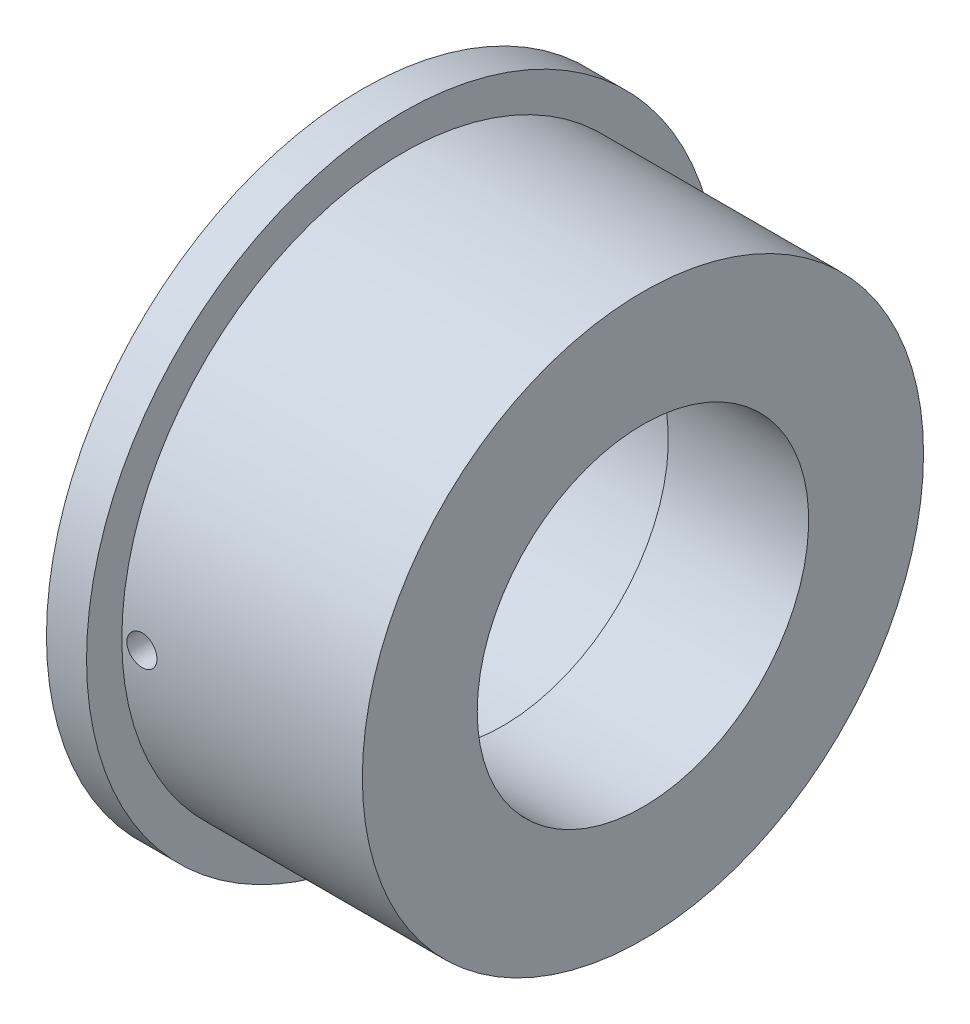
SolidWorks part; units mm, degrees
ref_plane "Front Plane" through (0, 0, 0) normal (0, 0, 1) x (1, 0, 0)
ref_plane "Top Plane" through (0, 0, 0) normal (0, 1, 0) x (1, 0, 0)
ref_plane "Right Plane" through (0, 0, 0) normal (1, 0, 0) x (0, 0, -1)
sketch "Sketch0" plane through (0, 0, 0) normal (0, 0, 1) x (1, 0, 0)
  line L0 (-44.45, 0) -> (0, 0) construction
  line L2 (-38.1, 44.45) -> (-38.1, -44.45) construction
  line L3 (-38.1, 50.038) -> (-38.1, -50.038) construction
  line L4 (-44.45, 34.3535) -> (-44.45, -34.3535) construction
  line L5 (-22.225, 30.099) -> (-44.45, 30.2895) construction
  line L6 (-22.225, 30.099) -> (-22.225, -30.099) construction
  line L7 (-22.225, -30.099) -> (-44.45, -30.2895) construction
  line L8 (-44.45, 30.2895) -> (-44.45, -30.2895) construction
  line L14 (-22.225, 26.2509) -> (-22.225, -26.2509) construction
  line L15 (-22.225, -26.2509) -> (-22.225, -30.3149) construction
  line L16 (-44.45, -30.2895) -> (-44.45, -34.3535) construction
  line L21 (-44.45, 0) -> (-22.225, 0) construction
  point P12 (-38.1, 0)
  dimension "A" = 44.45
  dimension "OD A 2" = 60.579
  dimension "OD B 2" = 60.198
  dimension "ID 2" = 52.5018
  dimension "H 2" = 4.064
  dimension "B" = 22.225
  dimension "Pipe OD 1" = 88.9
  dimension "C 1" = 38.1
  dimension "H 1" = 5.588
sketch "Sketch1" plane through (0, 0, 0) normal (0, 0, 1) x (1, 0, 0)
  line L0 (-44.45, 0) -> (0, 0) construction
  line L1 (-44.45, 0) -> (0, 0) construction
  line L2 (-38.1, -44.45) -> (0, -44.45)
  line L3 (0, -26.2509) -> (0, -44.45)
  line L4 (-44.45, -34.3535) -> (-44.45, -30.2895)
  line L5 (-44.45, -30.2895) -> (-22.225, -30.099)
  line L6 (0, 0) -> (0, -26.2509) construction
  line L7 (-44.45, -34.3535) -> (-44.45, -50.038)
  line L8 (-22.225, -26.2509) -> (-22.225, -30.099)
  line L9 (-44.45, -50.038) -> (-38.1, -50.038)
  line L10 (-38.1, -50.038) -> (-38.1, -44.45)
  line L11 (-22.225, -26.2509) -> (0, -26.2509)
  line L12 (-38.1, 44.45) -> (-38.1, -44.45) construction
revolve "Revolve1" add sketch "Sketch1" angle 360 about L1
sketch "Sketch2" plane through (0, 0, 0) normal (0, 0, 1) x (1, 0, 0)
  circle A0 centre (-34.925, 0) radius 2.3812
  dimension "D1" = 4.7625
  dimension "D2" = 34.925
extrude "Cut-Extrude1" cut sketch "Sketch2" along normal through all both and the other way through all
